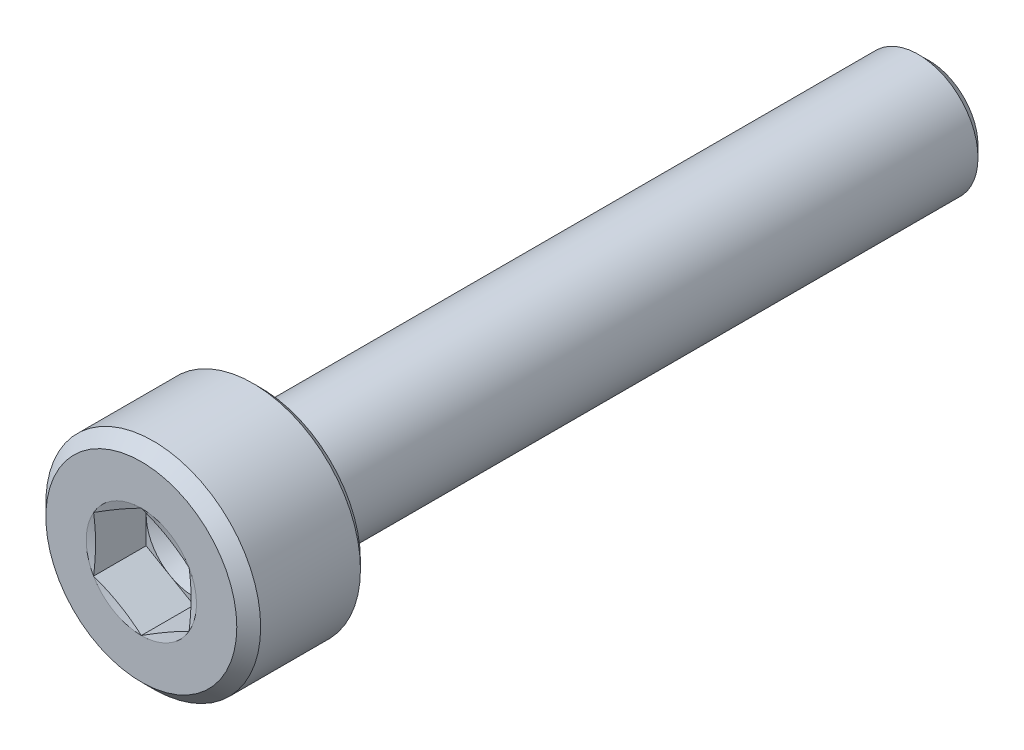
SolidWorks part; units mm, degrees
ref_plane "Front Plane" through (0, 0, 0) normal (0, 0, 1) x (1, 0, 0)
ref_plane "Top Plane" through (0, 0, 0) normal (0, 1, 0) x (1, 0, 0)
ref_plane "Right Plane" through (0, 0, 0) normal (1, 0, 0) x (0, 0, -1)
sketch "Sketch1" plane through (0, 0, 0) normal (1, 0, 0) x (0, 0, -1)
  line L0 (0, 0) -> (12.9407, 0) construction
  line L1 (0, 0) -> (0, 2)
  line L2 (0, 2) -> (0.25, 2.25)
  line L3 (0.25, 2.25) -> (2.34, 2.25)
  line L4 (2.5, 2.09) -> (2.5, 1.55)
  line L5 (3.01, 1.25) -> (16.275, 1.25)
  line L6 (16.275, 1.25) -> (16.5, 1.025)
  line L7 (16.5, 1.025) -> (16.5, 0)
  line L8 (16.5, 0) -> (0, 0)
  line L9 (2.34, 2.25) -> (2.5, 2.09)
  line L10 (2.9662, 1.2601) -> (2.5562, 1.4601)
  arc A2 (3.01, 1.25) -> (2.9662, 1.2601) centre (3.01, 1.35) cw
  arc A3 (2.5562, 1.4601) -> (2.5, 1.55) centre (2.6, 1.55) cw
  point P6 (2.5, 2.25)
  dimension "R2" = 0.1
  dimension "R1" = 0.1
  dimension "D1" = 45
  dimension "DK" = 4.5
  dimension "D3" = 45
  dimension "length" = 14
  dimension "K" = 2.5
  dimension "V" = 0.25
  dimension "HOLESIZE" = 2.5
  dimension "D4" = 2.05
  dimension "D5" = 45
  dimension "DW" = 4.18
  dimension "F" = 0.51
  dimension "DA" = 3.1
revolve "Revolve1" add sketch "Sketch1" angle 360 about L0
cosmetic thread "Cosmetic Thread1" parameters "D1"=12.65, "D2"=2.5
sketch "Sketch2" plane through (0, 0, 0) normal (0, 0, 1) x (1, 0, 0)
  line L0 (0, 0) -> (0, 1.1547) construction
  line L2 (0, 1.1547) -> (-1, 0.5774)
  line L3 (-1, 0.5774) -> (-1, -0.5774)
  line L4 (-1, -0.5774) -> (0, -1.1547)
  line L5 (0, -1.1547) -> (1, -0.5774)
  line L6 (1, -0.5774) -> (1, 0.5774)
  line L7 (1, 0.5774) -> (0, 1.1547)
  circle A0 centre (0, 0) radius 1 construction
  dimension "S" = 2
extrude "Cut-Extrude1" cut sketch "Sketch2" against normal blind 1.1
sketch "Sketch3" plane through (0, 0, 0) normal (1, 0, 0) x (0, 0, -1)
  line L0 (1.1, 0) -> (16.5, 0) construction
  line L1 (16.5, -1.025) -> (16.5, 1.025) construction
  line L2 (1.1, 0) -> (1.1, 1)
  line L4 (1.1, 1) -> (1.6774, 0)
  line L5 (1.6774, 0) -> (1.1, 0)
  line L6 (0, 2) -> (0, -2) construction
  dimension "DRILLANG" = 60
  dimension "DRILL DEPTH" = 1.1
  dimension "S2" = 2
revolve "Cut-Revolve2" cut sketch "Sketch3" angle 360 about L0
sketch "Sketch4" plane through (0, 0, 0) normal (1, 0, 0) x (0, 0, -1)
  line L0 (0, 0) -> (4.6121, 0) construction
  line L1 (0, 1.1547) -> (0, 1)
  line L2 (0, 2) -> (0, -2) construction
  line L3 (0, 1) -> (0.0415, 1)
  line L4 (0.0415, 1) -> (0, 1.1547)
  point P12 (0.0207, 1)
  dimension "D1" = 2
  dimension "D2" = 15
revolve "Cut-Revolve3" cut sketch "Sketch4" angle 360 about L0
